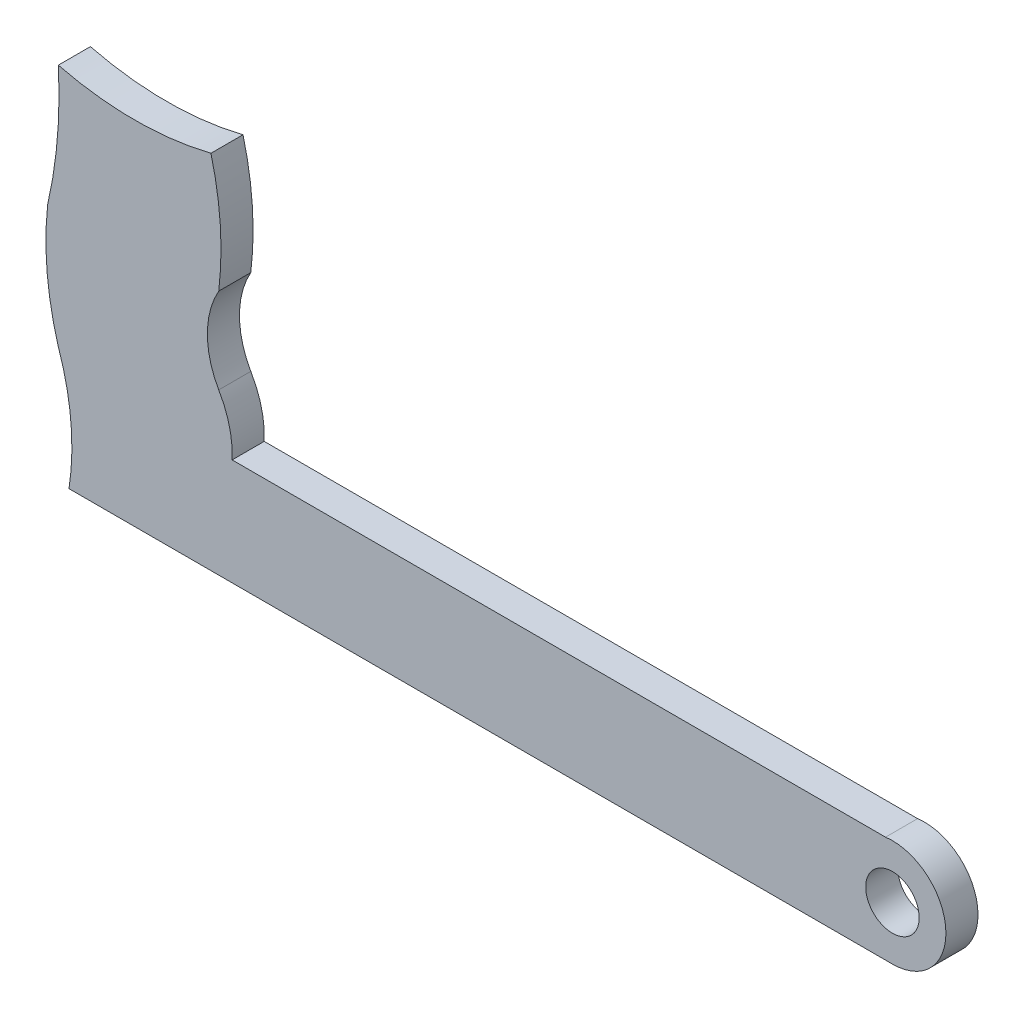
SolidWorks part; units mm, degrees
ref_plane "Alzado" through (0, 0, 0) normal (0, 0, 1) x (1, 0, 0)
ref_plane "Planta" through (0, 0, 0) normal (0, 1, 0) x (1, 0, 0)
ref_plane "Vista lateral" through (0, 0, 0) normal (1, 0, 0) x (0, 0, -1)
sketch "Model" plane through (0, 0, 0) normal (0, 0, 1) x (1, 0, 0)
  line L0 (11.0801, 12.1) -> (32.6262, 12.1)
  line L1 (32.6262, 12.1) -> (54.0875, 12.1)
  line L2 (54.0875, 12.1) -> (88.0801, 12.1)
  line L3 (87.4335, 22.058) -> (26.3349, 22.058)
  circle A0 centre (88.0801, 17.1) radius 2.5
  arc A1 (88.0801, 12.1) -> (87.4335, 22.058) centre (88.0801, 17.1) ccw
  arc A2 (26.3349, 22.058) -> (25.0801, 27.1) centre (17.2986, 22.4864) ccw
  arc A3 (25.0801, 35.1) -> (25.0801, 27.1) centre (32.0801, 31.1) ccw
  arc A4 (25.0801, 35.1) -> (24.3506, 45.9) centre (-3.4124, 38.6) ccw
  arc A5 (10.0801, 45.9) -> (24.3506, 45.9) centre (17.2154, 74.471) ccw
  arc A6 (9.0801, 34.1) -> (10.0801, 45.9) centre (-31.7197, 43.5) ccw
  arc A7 (9.0801, 34.1) -> (10.0801, 23.1) centre (37.0801, 31.1) ccw
  arc A8 (11.0801, 12.1) -> (10.0801, 23.1) centre (-11.4199, 15.6) ccw
  point P22 (11.0984, 12.22)
extrude "Saliente-Extruir1" add sketch "Model" along normal blind 3
